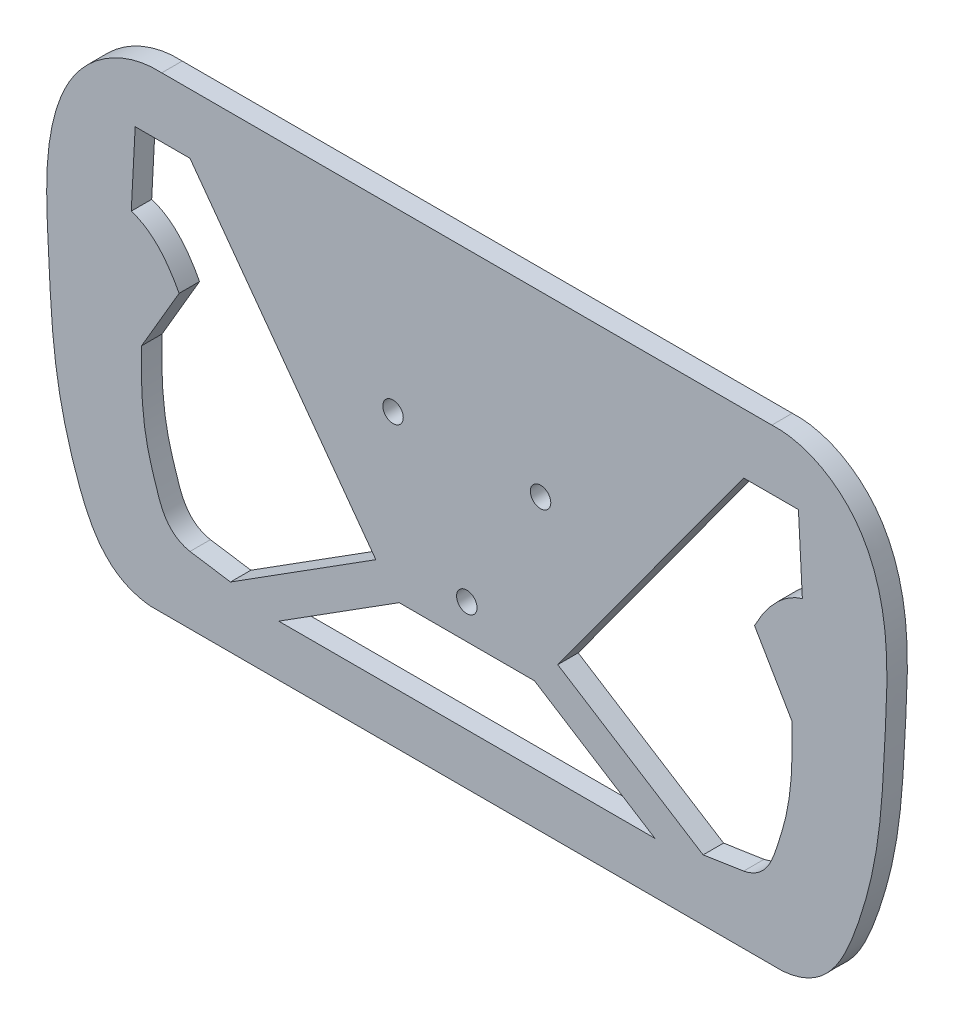
SolidWorks part; units mm, degrees
ref_plane "Front Plane" through (0, 0, 0) normal (0, 0, 1) x (1, 0, 0)
ref_plane "Top Plane" through (0, 0, 0) normal (0, 1, 0) x (1, 0, 0)
ref_plane "Right Plane" through (0, 0, 0) normal (1, 0, 0) x (0, 0, -1)
sketch "Sketch2" plane through (0, 0, 0) normal (0, 0, 1) x (1, 0, 0)
  line L0 (-37.2099, 73.2438) -> (312.1235, 73.2438) construction
sketch "Sketch1" plane through (0, 0, 0) normal (0, 0, 1) x (1, 0, 0)
  line L0 (0, 0) -> (0, 4.7682) construction
  line L2 (-21.6506, 12.5) -> (0, -25) construction
  line L3 (0, -25) -> (21.6506, 12.5) construction
  line L4 (21.6506, 12.5) -> (-21.6506, 12.5) construction
  line L16 (97.3439, 47.1313) -> (98.4999, 25.0798)
  line L17 (98.4999, 25.0798) -> (84.451, 11.2087) construction
  line L18 (84.451, 11.2087) -> (95.4767, -7.6417)
  line L19 (92.8419, -72.5039) -> (-92.8419, -72.5039)
  line L20 (97.3439, 47.1313) -> (81.2606, 47.1313)
  line L21 (81.2606, 47.1313) -> (26.6942, -27.6178)
  line L22 (26.6942, -27.6178) -> (69.37, -54.6286)
  line L23 (69.37, -54.6286) -> (81.2606, -52.808)
  line L24 (-19.8616, -35.128) -> (19.8616, -35.128)
  line L25 (19.8616, -35.128) -> (55.2146, -57.5039)
  line L26 (55.2146, -57.5039) -> (-55.2146, -57.5039)
  line L27 (-89.5434, 64.7224) -> (89.5434, 64.7224)
  line L29 (-125, 75) -> (125, 75) construction
  line L30 (-125, 75) -> (-125, -75) construction
  line L31 (-125, -75) -> (125, -75) construction
  line L32 (125, 75) -> (125, -75) construction
  line L34 (-97.3439, 47.1313) -> (-81.2606, 47.1313)
  line L35 (-97.3439, 47.1313) -> (-98.4999, 25.0798)
  line L36 (-84.451, 11.2087) -> (-95.4767, -7.6417)
  line L37 (-69.37, -54.6286) -> (-81.2606, -52.808)
  line L38 (-26.6942, -27.6178) -> (-69.37, -54.6286)
  line L39 (-81.2606, 47.1313) -> (-26.6942, -27.6178)
  line L41 (-19.8616, -35.128) -> (-55.2146, -57.5039)
  circle A2 centre (-21.6506, 12.5) radius 3
  circle A3 centre (21.6506, 12.5) radius 3
  circle A4 centre (0, -25) radius 3
  circle A5 centre (0, 0) radius 25 construction
  spline S0 degree 3 poles (95.4767, -7.6417) (95.6524, -15.8577) (95.5024, -27.4781) (90.6196, -43.3006) (87.8145, -51.4531) (81.2606, -52.808) knots 0 0 0 0 0.501053 0.67815 1 1 1 1
  spline S1 degree 3 poles (89.5434, 64.7224) (98.9087, 65.2213) (113.8148, 57.2845) (124.4226, 32.0211) (122.7713, 4.0381) (121.5286, -25.8175) (114.3389, -53.6273) (105.5681, -71.3122) (92.8419, -72.5039) knots 0 0 0 0 0.167204 0.270778 0.479134 0.66479 0.809328 1 1 1 1
  spline S2 degree 3 poles (98.4999, 25.0798) (91.8937, 23.0577) (87.5138, 17.0133) (84.451, 11.2087) knots 0 0 0 0 1 1 1 1
  spline S3 degree 3 poles (-98.4999, 25.0798) (-91.8937, 23.0577) (-87.5138, 17.0133) (-84.451, 11.2087) knots 0 0 0 0 1 1 1 1
  spline S4 degree 3 poles (-95.4767, -7.6417) (-95.6524, -15.8577) (-95.5024, -27.4781) (-90.6196, -43.3006) (-87.8145, -51.4531) (-81.2606, -52.808) knots 0 0 0 0 0.501053 0.67815 1 1 1 1
  spline S5 degree 3 poles (-89.5434, 64.7224) (-98.9087, 65.2213) (-113.8148, 57.2845) (-124.4226, 32.0211) (-122.7713, 4.0381) (-121.5286, -25.8175) (-114.3389, -53.6273) (-105.5681, -71.3122) (-92.8419, -72.5039) knots 0 0 0 0 0.167204 0.270778 0.479134 0.66479 0.809328 1 1 1 1
  point P16 (0, 64.7224)
  point P22 (0, -72.5039)
  point P33 (55.1646, -56.8037)
  point P34 (125, 0)
  point P36 (0, 75)
  point P70 (0, -57.5039)
  point P71 (0, -35.128)
  point P72 (55.2146, -57.5039)
  point P73 (30.4972, -28.1364)
  point P74 (17.6189, -31.248)
  point P75 (26.6942, -27.6178)
  dimension "D1" = 250
  dimension "D2" = 6
  dimension "D3" = 50
  dimension "D5" = 15
  dimension "D4" = 150
  dimension "D6" = 10
extrude "Boss-Extrude1" add sketch "Sketch1" along normal blind 6
